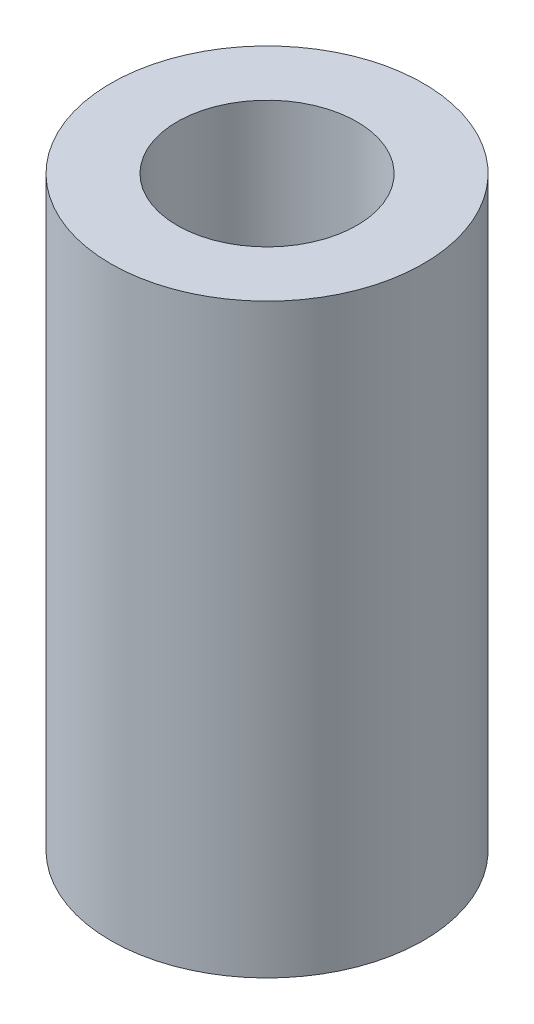
SolidWorks part; units mm, degrees
ref_plane "Front Plane" through (0, 0, 0) normal (0, 0, 1) x (1, 0, 0)
ref_plane "Top Plane" through (0, 0, 0) normal (0, 1, 0) x (1, 0, 0)
ref_plane "Right Plane" through (0, 0, 0) normal (1, 0, 0) x (0, 0, -1)
sketch "Sketch1" plane through (0, 0, 0) normal (0, 1, 0) x (1, 0, 0)
  circle A0 centre (0, 0) radius 2.3
  circle A1 centre (0, 0) radius 4
  dimension "D1" = 8
  dimension "D2" = 4.6
extrude "Boss-Extrude1" add sketch "Sketch1" along normal blind 15
